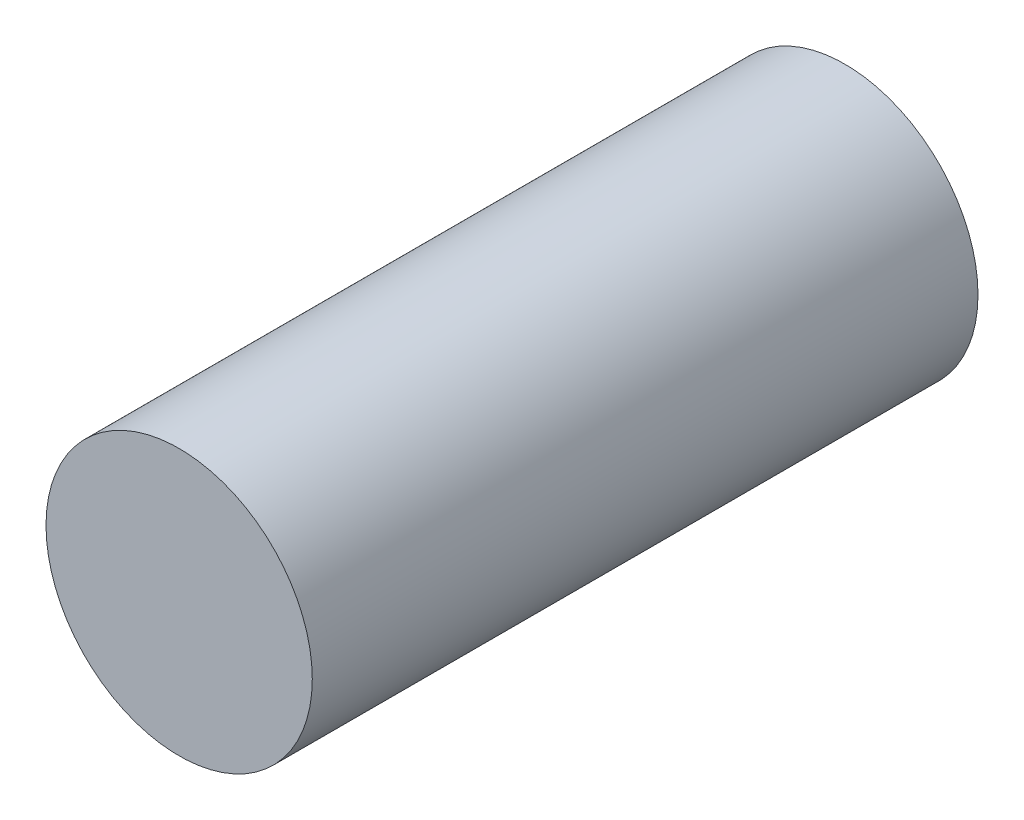
SolidWorks part; units mm, degrees
ref_plane "Front Plane" through (0, 0, 0) normal (0, 0, 1) x (1, 0, 0)
ref_plane "Top Plane" through (0, 0, 0) normal (0, 1, 0) x (1, 0, 0)
ref_plane "Right Plane" through (0, 0, 0) normal (1, 0, 0) x (0, 0, -1)
sketch "Sketch1" plane through (0, 0, 0) normal (0, 0, 1) x (1, 0, 0)
  circle A0 centre (-34.0583, 35.9011) radius 6.35
  dimension "D1" = 12.7
extrude "Boss-Extrude1" add sketch "Sketch1" along normal blind 31.75
